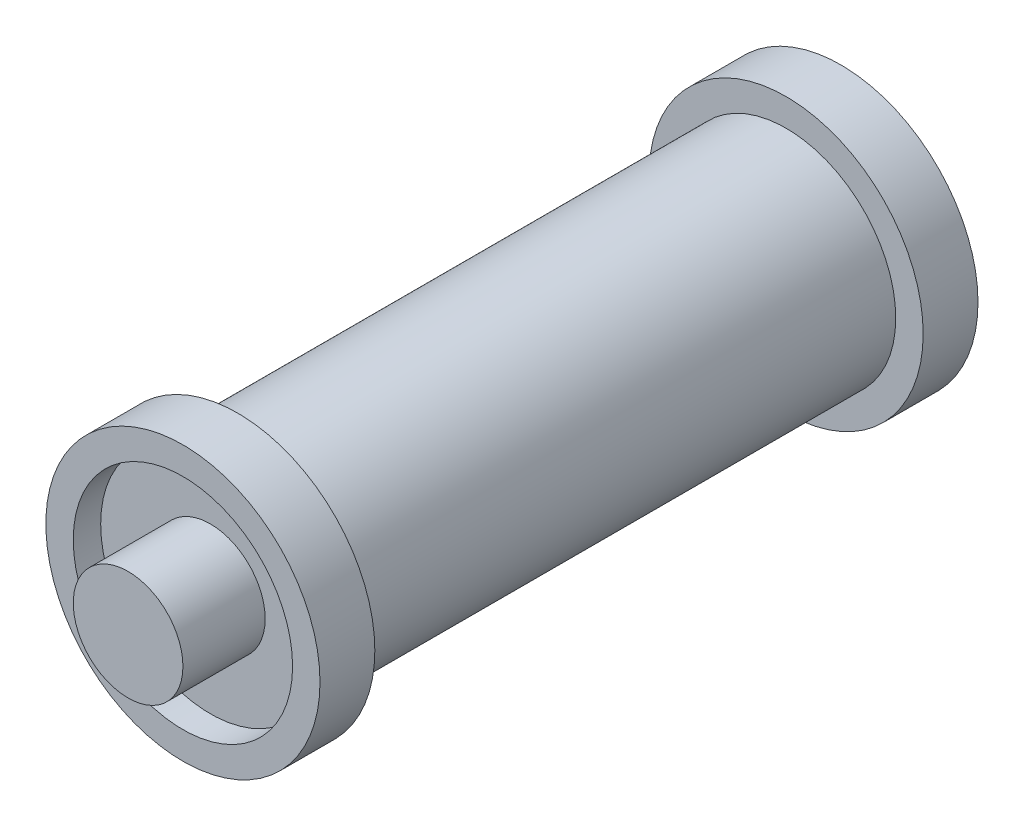
SolidWorks part; units mm, degrees
ref_plane "Alzado" through (0, 0, 0) normal (0, 0, 1) x (1, 0, 0)
ref_plane "Planta" through (0, 0, 0) normal (0, 1, 0) x (1, 0, 0)
ref_plane "Vista lateral" through (0, 0, 0) normal (1, 0, 0) x (0, 0, -1)
sketch "Croquis1" plane through (0, 0, 0) normal (0, 0, 1) x (1, 0, 0)
  circle A0 centre (0, 0) radius 5
  dimension "D1" = 10
extrude "Extruir1" add sketch "Croquis1" along normal blind 2
shell "Vaciado1" thickness 1
sketch "Croquis2" plane through (0, 0, 0) normal (0, 0, -1) x (-1, 0, 0)
  circle A0 centre (0, 0) radius 4
  dimension "D1" = 8
extrude "Extruir2" add sketch "Croquis2" along normal blind 10
mirror "Simetría3" about plane through (0, 0, -10) normal (0, 0, -1) of bodies 102
sketch "Croquis4" plane through (0, 0, 1) normal (0, 0, 1) x (1, 0, 0)
  circle A0 centre (0, 0) radius 2
extrude "Extruir4" add sketch "Croquis4" along normal blind 3
